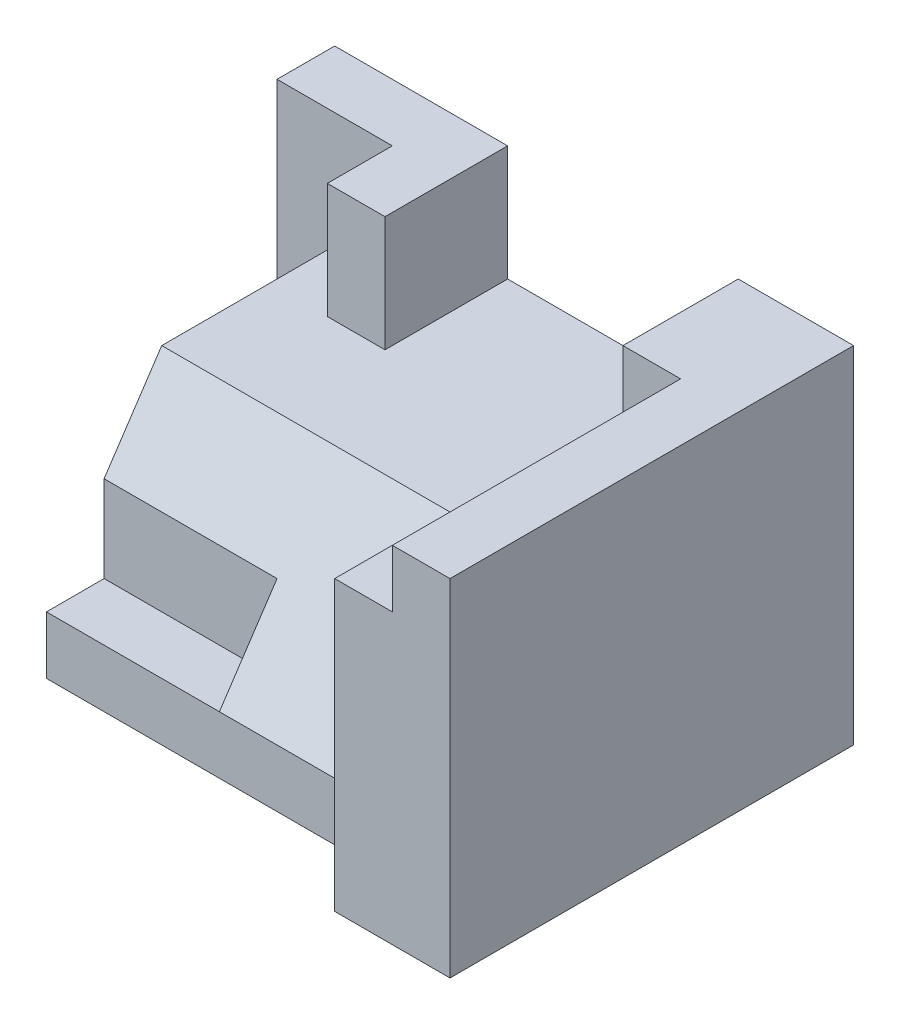
SolidWorks part; units mm, degrees
ref_plane "Front Plane" through (0, 0, 0) normal (0, 0, 1) x (1, 0, 0)
ref_plane "Top Plane" through (0, 0, 0) normal (0, 1, 0) x (1, 0, 0)
ref_plane "Right Plane" through (0, 0, 0) normal (1, 0, 0) x (0, 0, -1)
sketch "Sketch1" plane through (0, 0, 0) normal (0, 1, 0) x (1, 0, 0)
  line L1 (0, 0) -> (9, 0)
  line L2 (0, 0) -> (0, 7)
  line L3 (0, 7) -> (9, 7)
  line L4 (9, 0) -> (9, 7)
  dimension "D1" = 7
  dimension "D2" = 9
extrude "Boss-Extrude1" add sketch "Sketch1" along normal blind 6
sketch "Sketch2" plane through (0, 0, 0) normal (-1, 0, 0) x (0, 0, 1)
  line L0 (0, 0) -> (-1, 0)
  line L1 (-7, 0) -> (0, 0) construction
  line L2 (-1, 0) -> (-1, 1)
  line L3 (-1, 1) -> (-3, 4)
  line L4 (-3, 4) -> (-6, 4)
  line L5 (-6, 4) -> (-6, 6)
  line L6 (-7, 6) -> (0, 6) construction
  line L7 (-6, 6) -> (0, 6)
  line L9 (0, 6) -> (0, 0)
  dimension "D2" = 3
  dimension "D3" = 1
  dimension "D4" = 1
  dimension "D5" = 2
extrude "Cut-Extrude1" cut sketch "Sketch2" against normal blind 7
sketch "Sketch3" plane through (0, 0, 0) normal (-1, 0, 0) x (0, 0, 1)
  line L1 (-6, 4) -> (-1, 4)
  line L2 (-6, 4) -> (-6, 0)
  line L3 (-6, 0) -> (-1, 0)
  line L4 (-1, 4) -> (-1, 0)
extrude "Cut-Extrude2" cut sketch "Sketch3" against normal blind 1
sketch "Sketch4" plane through (0, 0, 0) normal (0, 0, 1) x (1, 0, 0)
  line L1 (7, 6) -> (8, 6)
  line L2 (7, 6) -> (7, 5)
  line L3 (7, 5) -> (8, 5)
  line L4 (8, 6) -> (8, 5)
  dimension "D1" = 1
  dimension "D2" = 1
extrude "Cut-Extrude3" cut sketch "Sketch4" against normal blind 5
sketch "Sketch5" plane through (1, 0, 0) normal (-1, 0, 0) x (0, 0, 1)
  line L1 (-1, 1) -> (-2, 1)
  line L2 (-1, 1) -> (-1, 2.5)
  line L3 (-1, 2.5) -> (-2, 2.5)
  line L4 (-2, 1) -> (-2, 2.5)
  dimension "D1" = 1.5
  dimension "D2" = 1
extrude "Cut-Extrude4" cut sketch "Sketch5" against normal blind 3
sketch "Sketch6" plane through (0, 6, 0) normal (0, 1, 0) x (1, 0, 0)
  line L0 (9, 7) -> (0, 7) construction
  line L1 (7, 6) -> (3, 6)
  line L2 (7, 6) -> (7, 7)
  line L3 (7, 7) -> (3, 7)
  line L4 (3, 6) -> (3, 7)
  dimension "D1" = 4
extrude "Cut-Extrude5" cut sketch "Sketch6" against normal blind 2
sketch "Sketch7" plane through (0, 4, 0) normal (0, 1, 0) x (1, 0, 0)
  line L1 (3, 6) -> (2, 6)
  line L2 (3, 6) -> (3, 4.8725)
  line L3 (3, 4.8725) -> (2, 4.8725)
  line L4 (2, 6) -> (2, 4.8725)
  dimension "D1" = 1
extrude "Boss-Extrude2" add sketch "Sketch7" along normal blind 2
